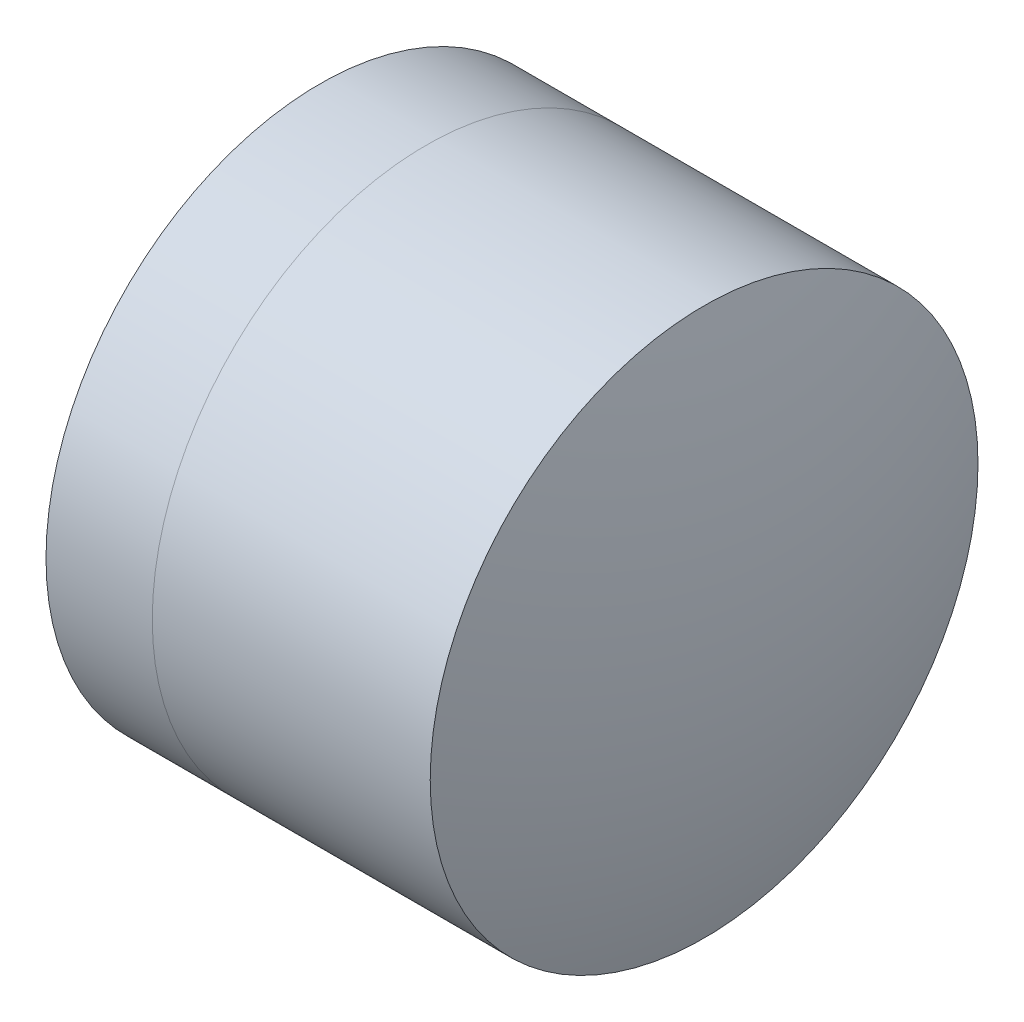
SolidWorks part; units mm, degrees
ref_plane "前视基准面" through (0, 0, 0) normal (0, 0, 1) x (1, 0, 0)
ref_plane "上视基准面" through (0, 0, 0) normal (0, 1, 0) x (1, 0, 0)
ref_plane "右视基准面" through (0, 0, 0) normal (1, 0, 0) x (0, 0, -1)
sketch "草图1" plane through (0, 0, 0) normal (0, 1, 0) x (1, 0, 0)
  line L0 (-0.8161, 0) -> (5.6164, 0) construction
  line L1 (2.5681, -3.15) -> (3.7903, -3.15)
  line L2 (2.5681, 3.15) -> (3.7903, 3.15)
  arc A0 (3.7903, -3.15) -> (3.7903, 3.15) centre (1.0946, 0) ccw
  arc A1 (2.5681, 3.15) -> (2.5681, -3.15) centre (8.6486, 0) ccw
  point P4 (5.6164, 0)
  point P10 (1.8006, 0)
  point P11 (5.2406, 0)
  dimension "D3" = 6.848
  dimension "D4" = 4.146
  dimension "D1" = 3.15
  dimension "D2" = 3.15
  dimension "D5" = 3.44
revolve "旋转1" add sketch "草图1" angle 360 about L0
sketch "草图2" plane through (0, 0, 0) normal (0, 1, 0) x (1, 0, 0)
  line L0 (-0.5519, 0) -> (8.312, 0) construction
  line L2 (3.7903, 3.15) -> (6.9868, 3.15)
  line L3 (3.7903, -3.15) -> (6.9868, -3.15)
  arc A0 (6.9868, -3.15) -> (6.9868, 3.15) centre (-2.6094, 0) ccw
  arc A1 (3.7903, -3.15) -> (3.7903, 3.15) centre (1.0946, 0) ccw construction
  arc A2 (3.7903, -3.15) -> (3.7903, 3.15) centre (1.0946, 0) ccw
  point P4 (5.2406, 0)
  point P8 (7.4906, 0)
  point P9 (8.312, 0)
  dimension "D1" = 10.1
  dimension "D2" = 2.25
revolve "旋转3" add sketch "草图2" angle 360 about L0
